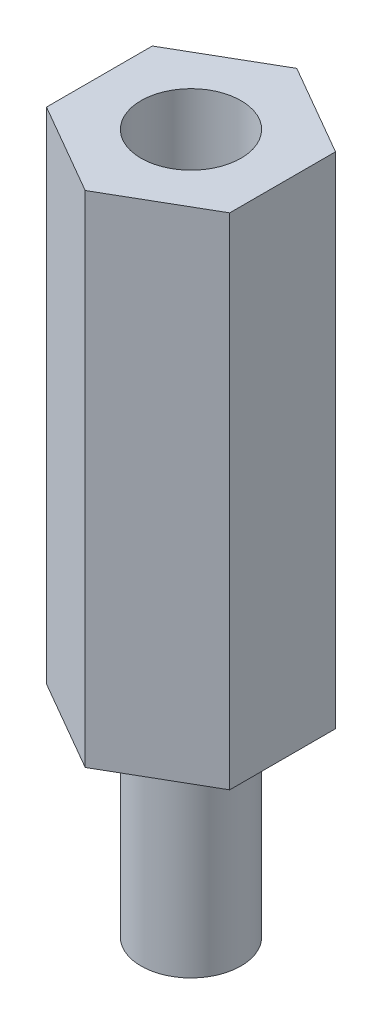
SolidWorks part; units mm, degrees
ref_plane "Alzado" through (0, 0, 0) normal (0, 0, 1) x (1, 0, 0)
ref_plane "Planta" through (0, 0, 0) normal (0, 1, 0) x (1, 0, 0)
ref_plane "Vista lateral" through (0, 0, 0) normal (1, 0, 0) x (0, 0, -1)
sketch "Croquis1" plane through (0, 0, 0) normal (0, 1, 0) x (1, 0, 0)
  line L1 (0, 3.1754) -> (-2.75, 1.5877)
  line L2 (-2.75, 1.5877) -> (-2.75, -1.5877)
  line L3 (-2.75, -1.5877) -> (0, -3.1754)
  line L4 (0, -3.1754) -> (2.75, -1.5877)
  line L5 (2.75, -1.5877) -> (2.75, 1.5877)
  line L6 (2.75, 1.5877) -> (0, 3.1754)
  circle A0 centre (0, 0) radius 2.75 construction
  dimension "D1" = 5.5
extrude "Saliente-Extruir1" add sketch "Croquis1" along normal blind 15
sketch "Croquis2" plane through (0, 0, 0) normal (0, -1, 0) x (1, 0, 0)
  circle A0 centre (0, 0) radius 1.5
  dimension "D1" = 3
extrude "Saliente-Extruir2" add sketch "Croquis2" along normal blind 6
sketch "Croquis3" plane through (0, 15, 0) normal (0, 1, 0) x (1, 0, 0)
  circle A0 centre (0, 0) radius 1.5
  dimension "D1" = 3
extrude "Cortar-Extruir1" cut sketch "Croquis3" against normal blind 6
